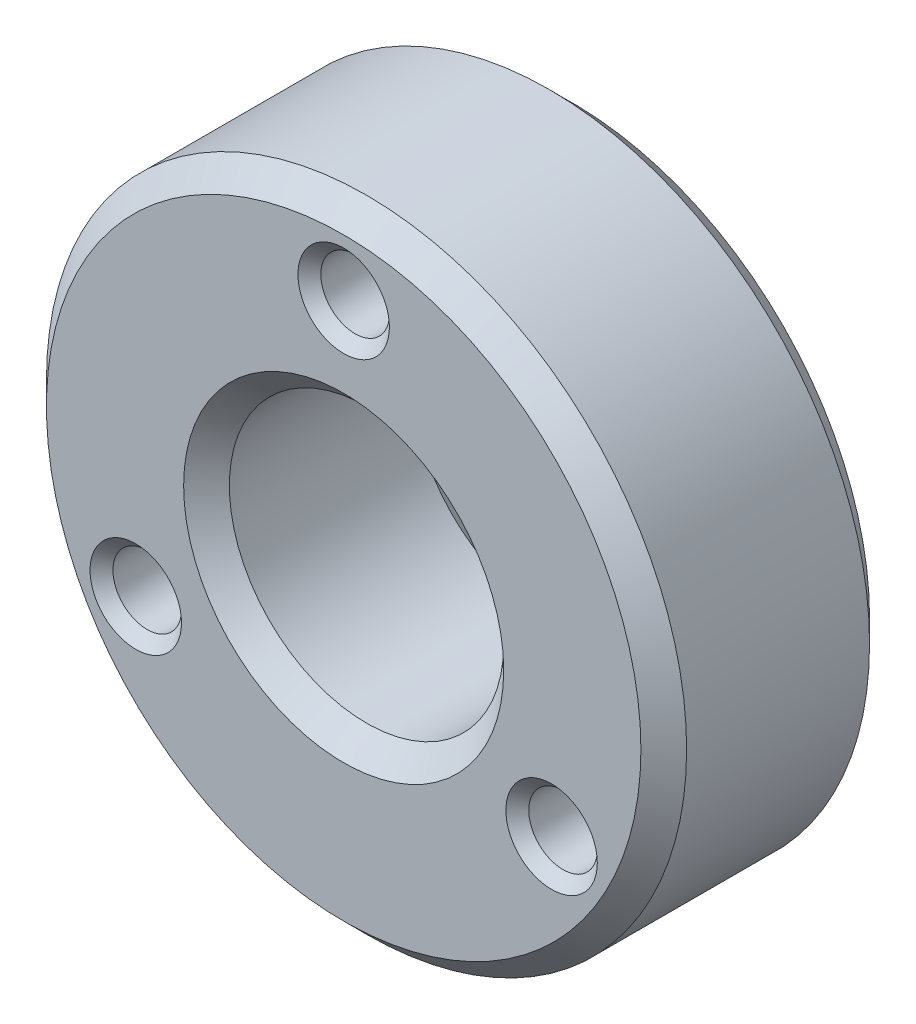
SolidWorks part; units mm, degrees
material "ABS PC"
ref_plane "Front" through (0, 0, 0) normal (0, 0, 1) x (1, 0, 0)
ref_plane "Top" through (0, 0, 0) normal (0, 1, 0) x (1, 0, 0)
ref_plane "Right" through (0, 0, 0) normal (1, 0, 0) x (0, 0, -1)
sketch "Sketch1" plane through (0, 0, 0) normal (0, 0, 1) x (1, 0, 0)
  line L0 (0, 10.5) -> (-9.0933, -5.25) construction
  line L1 (-9.0933, -5.25) -> (9.0933, -5.25) construction
  line L2 (9.0933, -5.25) -> (0, 10.5) construction
  line L3 (0, 10.5) -> (0, 0) construction
  line L4 (0, 0) -> (9.0933, -5.25) construction
  line L5 (0, 0) -> (-9.0933, -5.25) construction
  circle A0 centre (0, 0) radius 14
  circle A1 centre (0, 0) radius 6
  circle A2 centre (0, 10.5) radius 1.5
  circle A3 centre (9.0933, -5.25) radius 1.5
  circle A4 centre (-9.0933, -5.25) radius 1.5
  point P6 (0, 14)
  point P8 (0, 12)
  dimension "D1" = 28
  dimension "D2" = 12
  dimension "D3" = 3
  dimension "D4" = 2
  dimension "D5" = 3
extrude "Boss-Extrude1" add sketch "Sketch1" along normal blind 10
chamfer "Chamfer1" distance 1 angle 45 4 edges at (6, 0, 0) (6, 0, 10) (14, 0, 10) (14, 0, 0)
chamfer "Chamfer2" distance 0.5 angle 45 6 edges at (-7.5933, -5.25, 0) (10.5933, -5.25, 0) (1.5, 10.5, 0) (10.5933, -5.25, 10) (-7.5933, -5.25, 10) (1.5, 10.5, 10)
